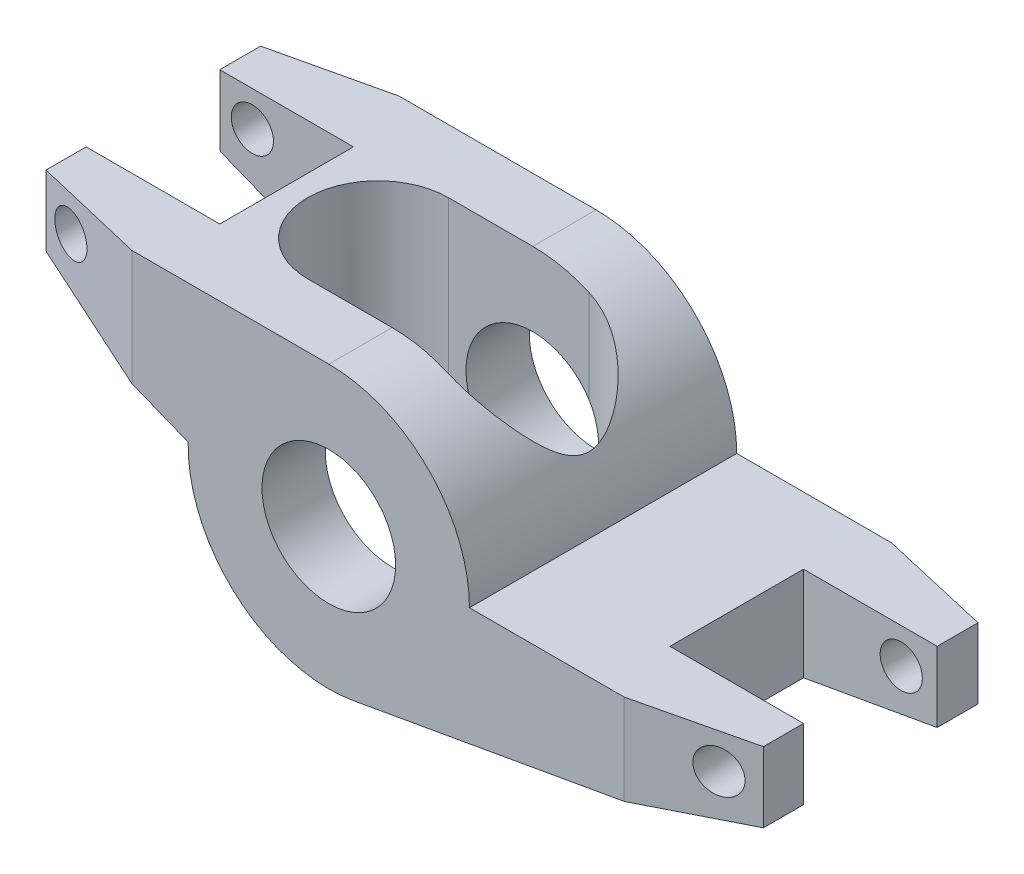
SolidWorks part; units mm, degrees
ref_plane "Front Plane" through (0, 0, 0) normal (0, 0, 1) x (1, 0, 0)
ref_plane "Top Plane" through (0, 0, 0) normal (0, 1, 0) x (1, 0, 0)
ref_plane "Right Plane" through (0, 0, 0) normal (1, 0, 0) x (0, 0, -1)
sketch "Sketch1" plane through (0, 0, 0) normal (0, 0, 1) x (1, 0, 0)
  line L0 (0, 10) -> (-22, 10)
  line L1 (-22, 10) -> (-22, 5)
  line L2 (-22, 5) -> (-9.998, 0.2)
  line L3 (10, 0) -> (29, 0)
  line L4 (29, 0) -> (29, -5)
  line L5 (29, -5) -> (1.7508, -9.8455)
  arc A0 (-9.998, 0.2) -> (1.7508, -9.8455) centre (0, 0) ccw
  circle A1 centre (0, 0) radius 4.75
  arc A2 (10, 0) -> (0, 10) centre (0, 0) ccw
  dimension "D1" = 9.5
  dimension "D2" = 20
  dimension "D3" = 22
  dimension "D4" = 9.8
  dimension "D5" = 5
  dimension "D6" = 51
extrude "Boss-Extrude1" add sketch "Sketch1" along normal mid plane 19
sketch "Sketch2" plane through (0, 0, 0) normal (0, 1, 0) x (1, 0, 0)
  line L0 (-22, -9.5) -> (-22, 9.5) construction
  line L1 (-31.5, 4.75) -> (-12.5, 4.75)
  line L2 (-31.5, 4.75) -> (-31.5, -4.75)
  line L3 (-31.5, -4.75) -> (-12.5, -4.75)
  line L4 (-12.5, 4.75) -> (-12.5, -4.75)
  line L5 (-31.5, 4.75) -> (-12.5, -4.75) construction
  line L6 (-31.5, -4.75) -> (-12.5, 4.75) construction
  line L7 (29, -9.5) -> (29, 9.5) construction
  line L8 (38.5, 4.75) -> (19.5, 4.75)
  line L9 (38.5, 4.75) -> (38.5, -4.75)
  line L10 (38.5, -4.75) -> (19.5, -4.75)
  line L11 (19.5, 4.75) -> (19.5, -4.75)
  line L12 (38.5, 4.75) -> (19.5, -4.75) construction
  line L13 (38.5, -4.75) -> (19.5, 4.75) construction
  line L14 (-6, 0) -> (4, 0) construction
  line L15 (-6, 0) -> (4, 0) construction
  line L16 (-6, 5) -> (4, 5)
  line L17 (-6, -5) -> (4, -5)
  arc A0 (-6, 5) -> (-6, -5) centre (-6, 0) ccw
  arc A1 (4, -5) -> (4, 5) centre (4, 0) ccw
  point P0 (-22, 0)
  point P7 (29, 0)
  point P17 (-1, 0)
  dimension "D7" = 5
  dimension "D1" = 9.5
  dimension "D2" = 19
  dimension "D3" = 19
  dimension "D4" = 9.5
  dimension "D5" = 16
  dimension "D6" = 10
extrude "Cut-Extrude1" cut sketch "Sketch2" against normal through all both and the other way through all
chamfer "Chamfer1" distance 8 angle 13.33 2 edges at (-22, 7.5, 9.5) (29, -2.5, 9.5)
chamfer "Chamfer2" distance 8 angle 13 2 edges at (29, -2.5, -9.5) (-22, 7.5, -9.5)
sketch "Sketch5" plane through (0, 0, 0) normal (0, 0, 1) x (1, 0, 0)
  circle A0 centre (-19.6846, 7.5) radius 1.5
  circle A1 centre (26.4462, -2.5) radius 1.5
extrude "Cut-Extrude2" cut sketch "Sketch5" against normal through all both and the other way through all
